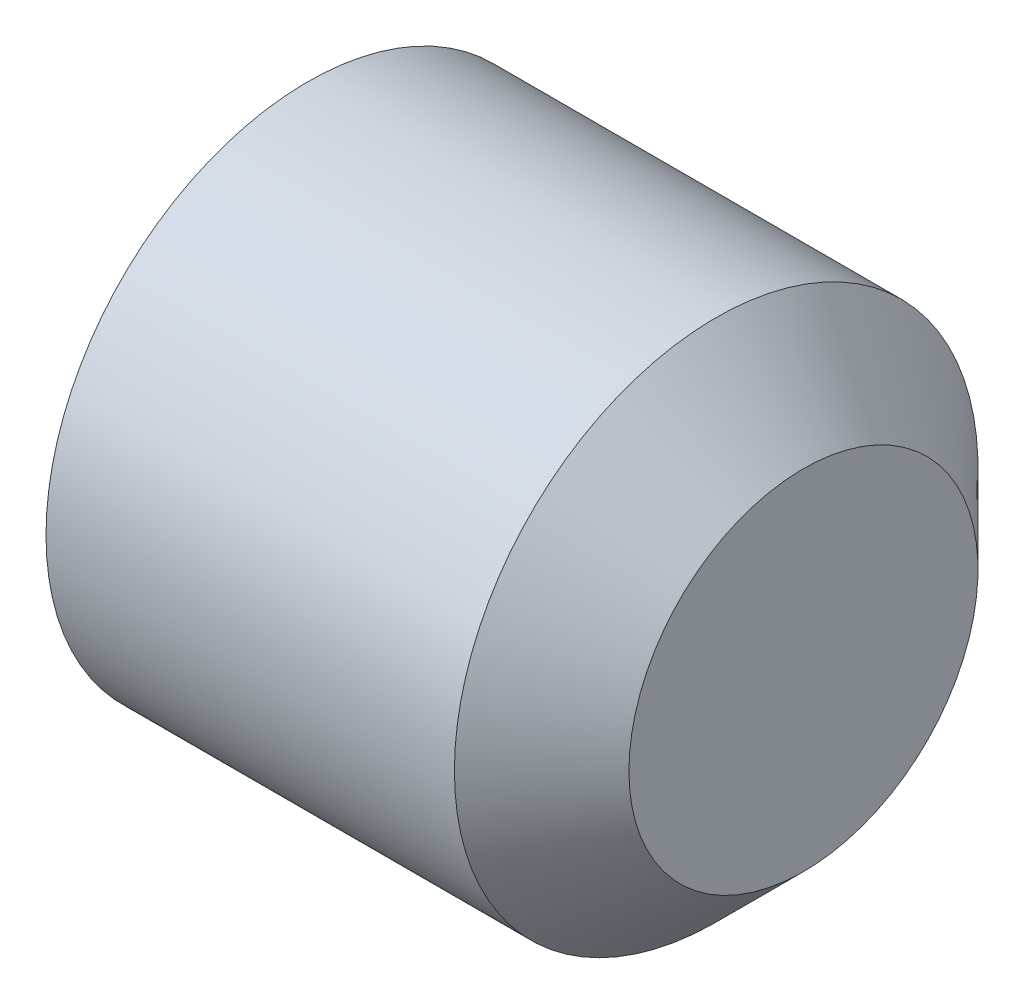
SolidWorks part; units mm, degrees
ref_plane "Спереди" through (0, 0, 0) normal (0, 0, 1) x (1, 0, 0)
ref_plane "Сверху" through (0, 0, 0) normal (0, 1, 0) x (1, 0, 0)
ref_plane "Справа" through (0, 0, 0) normal (1, 0, 0) x (0, 0, -1)
ref_plane "Плоскость1" through (0, 0, 0) normal (0, 0, -1) x (-1, 0, 0)
sketch "Эскиз1" plane through (0, 0, 0) normal (0, 0, -1) x (-1, 0, 0)
  line L0 (-6, 2) -> (-6, 0)
  line L1 (-6, 0) -> (0, 0)
  line L2 (0, 0) -> (0, 3)
  line L3 (0, 3) -> (-5, 3)
  line L4 (-5, 3) -> (-6, 2)
  line L6 (-6, 0) -> (0, 0) construction
  point P6 (0, 0)
  point P8 (-6.0682, 2)
  dimension "D1" = 3
  dimension "D2" = 6
  dimension "D3" = 45
  dimension "D4" = 2
revolve "Повернуть1" add sketch "Эскиз1" angle 360 about L6
sketch "Эскиз2" plane through (0, 0, 0) normal (-1, 0, 0) x (0, 0, 1)
  line L0 (1.7321, 0) -> (0.866, 1.5)
  line L1 (0.866, 1.5) -> (-0.866, 1.5)
  line L2 (-0.866, 1.5) -> (-1.7321, 0)
  line L3 (-1.7321, 0) -> (-0.866, -1.5)
  line L4 (-0.866, -1.5) -> (0.866, -1.5)
  line L5 (0.866, -1.5) -> (1.7321, 0)
extrude "Вырез-Вытянуть1" cut sketch "Эскиз2" against normal blind 2
chamfer "Фаска1" distance 0.5545 angle 30 1 edges at (0, 0, 3)
